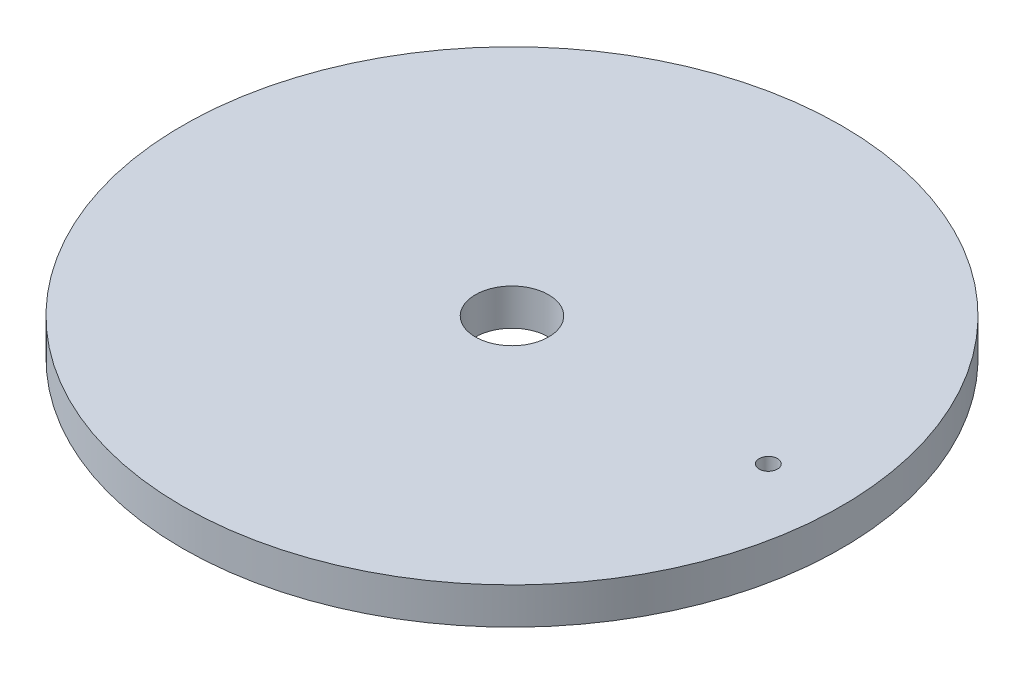
SolidWorks part; units mm, degrees
ref_plane "Front Plane" through (0, 0, 0) normal (0, 0, 1) x (1, 0, 0)
ref_plane "Top Plane" through (0, 0, 0) normal (0, 1, 0) x (1, 0, 0)
ref_plane "Right Plane" through (0, 0, 0) normal (1, 0, 0) x (0, 0, -1)
sketch "Sketch1" plane through (0, 0, 0) normal (0, 0, 1) x (1, 0, 0)
  line L0 (-6.35, 0) -> (-52.5145, 0)
  line L1 (-57.15, 0) -> (-57.15, 6.35)
  line L2 (-57.15, 6.35) -> (-6.35, 6.35)
  line L5 (-6.35, 6.35) -> (-6.35, 0)
  line L6 (0, 0) -> (0, 29.7484) construction
  line L7 (-57.15, 0) -> (-55.5625, 0)
  line L8 (-55.5625, 0) -> (-55.5625, 2.032)
  line L9 (-55.5625, 2.032) -> (-52.5145, 2.032)
  line L10 (-52.5145, 2.032) -> (-52.5145, 0)
  dimension "D1" = 6.35
  dimension "D2" = 57.15
  dimension "D4" = 6.35
  dimension "D6" = 2.032
  dimension "D7" = 3.048
  dimension "D8" = 1.5875
revolve "Revolve1" add sketch "Sketch1" angle 360 about L6
hole_wizard "1/8 (0.125) Diameter Hole1" positions "Sketch2" profile "Sketch4" hole size "1/8" standard "ANSI Inch"
sketch "Sketch2" plane through (0, 6.35, 0) normal (0, 1, 0) x (1, 0, 0)
  line L0 (0, 0) -> (44.45, 0) construction
  point P0 (44.45, 0)
  dimension "D1" = 44.45
sketch "Sketch4" plane through (44.45, 6.35, 0) normal (1, 0, 0) x (0, 0, 1)
  line L0 (0, 0) -> (0, 4.2559)
  line L1 (0, 4.2559) -> (1.5875, 3.302)
  line L2 (1.5875, 3.302) -> (1.5875, 0)
  line L5 (1.5875, 0) -> (0, 0)
  line L10 (0, 4.2559) -> (-1.5875, 3.302) construction
  line L11 (0, -6.35) -> (0, 107.95) construction
  dimension "Hole Dia." = 3.175
  dimension "Hole Depth" = 3.302
  dimension "Drill Angle" = 118
